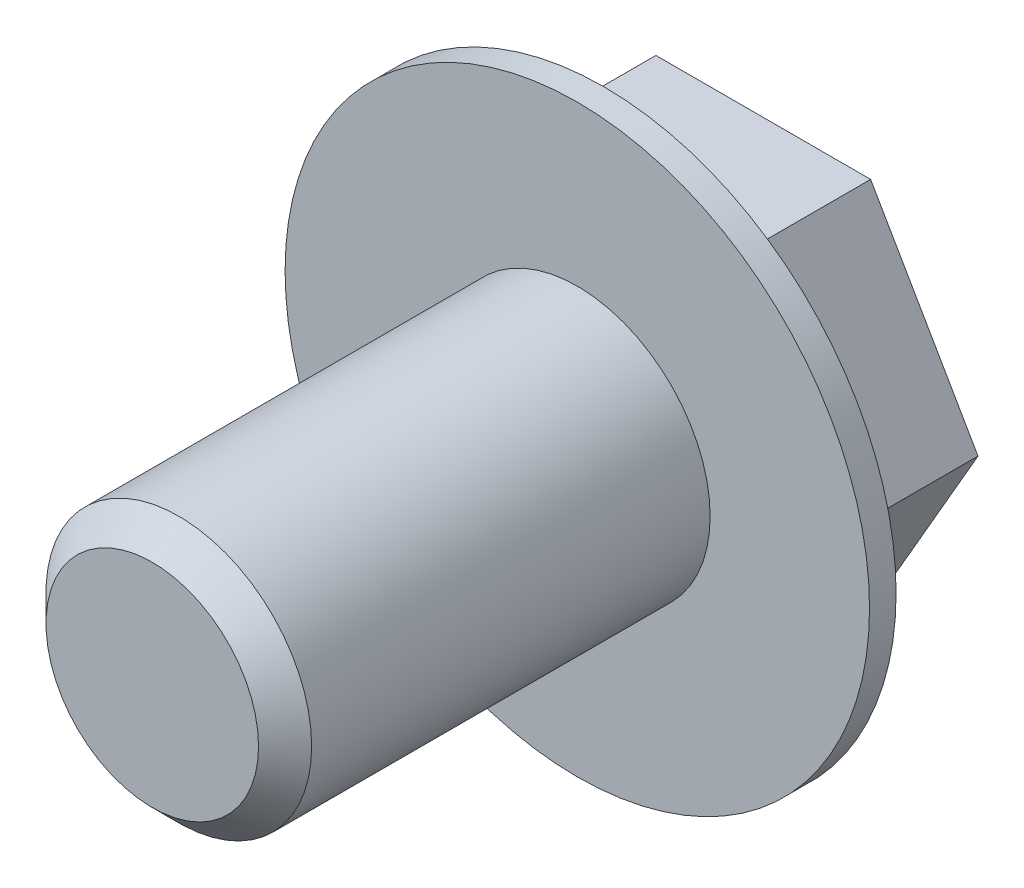
SolidWorks part; units mm, degrees
ref_plane "Front Plane" through (0, 0, 0) normal (0, 0, 1) x (1, 0, 0)
ref_plane "Top Plane" through (0, 0, 0) normal (0, 1, 0) x (1, 0, 0)
ref_plane "Right Plane" through (0, 0, 0) normal (1, 0, 0) x (0, 0, -1)
sketch "Sketch1" plane through (0, 0, 0) normal (0, 0, 1) x (1, 0, 0)
  circle A0 centre (0, 0) radius 2.5
  dimension "D1" = 5
extrude "Boss-Extrude1" add sketch "Sketch1" along normal blind 8
sketch "Sketch2" plane through (0, 0, 0) normal (0, 0, -1) x (-1, 0, 0)
  circle A0 centre (0, 0) radius 5.5
  dimension "D1" = 11
extrude "Boss-Extrude2" add sketch "Sketch2" along normal blind 0.5
sketch "Sketch3" plane through (0, 0, -0.5) normal (0, 0, -1) x (-1, 0, 0)
  line L1 (4.0415, 0) -> (2.0207, 3.5)
  line L2 (2.0207, 3.5) -> (-2.0207, 3.5)
  line L3 (-2.0207, 3.5) -> (-4.0415, 0)
  line L4 (-4.0415, 0) -> (-2.0207, -3.5)
  line L5 (-2.0207, -3.5) -> (2.0207, -3.5)
  line L6 (2.0207, -3.5) -> (4.0415, 0)
  circle A0 centre (0, 0) radius 3.5 construction
  dimension "D1" = 7
extrude "Boss-Extrude3" add sketch "Sketch3" along normal blind 3
chamfer "Chamfer3" distance 0.5 angle 45 1 edges at (2.5, 0, 8)
